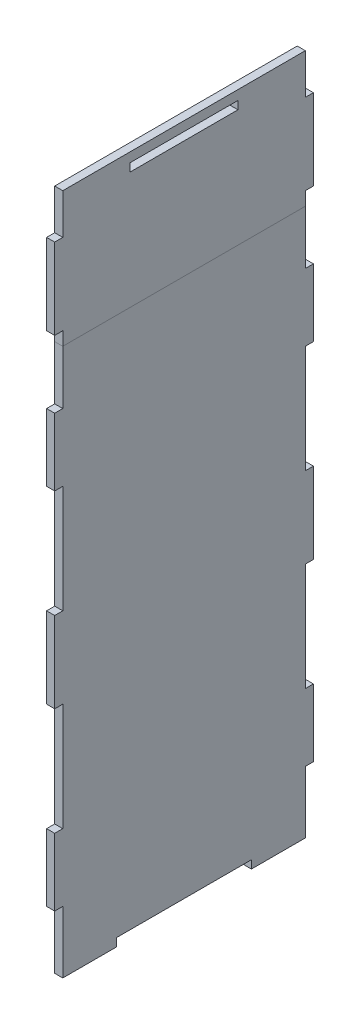
SolidWorks part; units mm, degrees
ref_plane "Front" through (0, 0, 0) normal (0, 0, 1) x (1, 0, 0)
ref_plane "Top" through (0, 0, 0) normal (0, 1, 0) x (1, 0, 0)
ref_plane "Right" through (0, 0, 0) normal (1, 0, 0) x (0, 0, -1)
sketch "Sketch1" plane through (0, 0, 0) normal (1, 0, 0) x (0, 0, -1)
  line L1 (0, 0) -> (90, 0)
  line L2 (0, 0) -> (0, 200)
  line L3 (0, 200) -> (90, 200)
  line L4 (90, 0) -> (90, 200)
  dimension "D1" = 200
  dimension "D2" = 90
extrude "Boss-Extrude1" add sketch "Sketch1" along normal blind 3
sketch "Sketch2" [suppressed] plane through (3, 0, 0) normal (1, 0, 0) x (0, 0, -1)
  line L0 (0, 0) -> (90, 0) construction
  line L1 (-3, 25) -> (0, 25)
  line L2 (-3, 25) -> (-3, 5)
  line L3 (-3, 5) -> (0, 5)
  line L4 (0, 25) -> (0, 5)
  line L5 (90, 25) -> (93, 25)
  line L6 (90, 25) -> (90, 5)
  line L7 (90, 5) -> (93, 5)
  line L8 (93, 25) -> (93, 5)
  line L9 (0, 200) -> (0, 0) construction
  line L10 (90, 0) -> (90, 200) construction
  line L12 (-3, 175) -> (0, 175)
  line L13 (-3, 175) -> (-3, 155)
  line L14 (-3, 155) -> (0, 155)
  line L15 (0, 175) -> (0, 155)
  line L16 (-3, 105) -> (0, 105)
  line L17 (-3, 105) -> (-3, 75)
  line L18 (-3, 75) -> (0, 75)
  line L19 (0, 105) -> (0, 75)
  line L20 (93, 175) -> (90, 175)
  line L21 (93, 175) -> (93, 155)
  line L22 (93, 155) -> (90, 155)
  line L23 (90, 175) -> (90, 155)
  line L24 (93, 105) -> (90, 105)
  line L25 (93, 105) -> (93, 75)
  line L26 (93, 75) -> (90, 75)
  line L27 (90, 105) -> (90, 75)
  dimension "D1" = 3
  dimension "D2" = 20
  dimension "D3" = 3
  dimension "D4" = 5
  dimension "D5" = 30
  dimension "D6" = 20
  dimension "D7" = 50
  dimension "D8" = 50
extrude "Boss-Extrude2" [suppressed] add sketch "Sketch2" against normal through all
sketch "Sketch3" [suppressed] plane through (3, 0, 0) normal (1, 0, 0) x (0, 0, -1)
  line L0 (10, 200) -> (15, 10)
  line L1 (15, 10) -> (75, 10)
  line L2 (75, 10) -> (80, 200)
  line L3 (80, 200) -> (10, 200)
  line L4 (90, 200) -> (0, 200) construction
  line L5 (0, 200) -> (0, 175) construction
  line L12 (0, 0) -> (90, 0) construction
  point P2 (45, 200)
  point P5 (45, 10)
  point P8 (45, 200)
  line M21 (90, 200) -> (0, 200)
  dimension "D1" = 10
  dimension "D2" = 15
  dimension "D3" = 10
extrude "Cut-Extrude1" [suppressed] cut sketch "Sketch3" against normal through all contours L1 L2 L0 M21
sketch "Sketch4" plane through (3, 0, 0) normal (1, 0, 0) x (0, 0, -1)
  line L0 (0, 200) -> (0, 0) construction
  line L1 (-3, 180) -> (0, 180)
  line L2 (-3, 180) -> (-3, 155)
  line L3 (-3, 155) -> (0, 155)
  line L4 (0, 180) -> (0, 155)
  line L5 (-3, 115) -> (0, 115)
  line L6 (-3, 115) -> (-3, 85)
  line L7 (-3, 85) -> (0, 85)
  line L8 (0, 115) -> (0, 85)
  line L9 (-3, 45) -> (0, 45)
  line L10 (-3, 45) -> (-3, 20)
  line L11 (-3, 20) -> (0, 20)
  line L12 (0, 45) -> (0, 20)
  line L13 (93, 20) -> (90, 20)
  line L14 (93, 20) -> (93, 45)
  line L15 (93, 45) -> (90, 45)
  line L16 (90, 20) -> (90, 45)
  line L17 (90, 85) -> (93, 85)
  line L18 (90, 85) -> (90, 115)
  line L19 (90, 115) -> (93, 115)
  line L20 (93, 85) -> (93, 115)
  line L21 (93, 155) -> (90, 155)
  line L22 (93, 155) -> (93, 180)
  line L23 (93, 180) -> (90, 180)
  line L24 (90, 155) -> (90, 180)
  line L25 (90, 0) -> (90, 200) construction
  line L26 (0, 0) -> (90, 0) construction
  line L27 (90, 200) -> (0, 200) construction
  point P28 (-3, 100)
  point P29 (0, 100)
  dimension "D1" = 3
  dimension "D5" = 30
  dimension "D6" = 20
  dimension "D2" = 3
  dimension "D3" = 25
  dimension "D4" = 25
  dimension "D7" = 20
extrude "Boss-Extrude3" add sketch "Sketch4" against normal through all
sketch "Sketch5" plane through (3, 0, 0) normal (1, 0, 0) x (0, 0, -1)
  line L0 (20, -1.5) -> (70, -1.5) construction
  line L1 (0, 0) -> (20, 0)
  line L2 (0, 0) -> (0, -3)
  line L3 (0, -3) -> (20, -3)
  line L4 (20, 0) -> (20, -3)
  line L5 (70, 0) -> (90, 0)
  line L6 (70, 0) -> (70, -3)
  line L7 (70, -3) -> (90, -3)
  line L8 (90, 0) -> (90, -3)
  line L9 (0, 0) -> (90, 0) construction
  point P13 (45, 0)
  point P14 (45, -1.5)
  dimension "D1" = 50
  dimension "D2" = 3
extrude "Boss-Extrude4" add sketch "Sketch5" against normal through all
sketch "Sketch6" plane through (3, 0, 0) normal (1, 0, 0) x (0, 0, -1)
  line L0 (90, 180) -> (90, 200) construction
  line L1 (0, 200) -> (90, 200)
  line L2 (0, 200) -> (0, 250)
  line L3 (0, 250) -> (90, 250)
  line L4 (90, 200) -> (90, 250)
  dimension "D1" = 50
extrude "Boss-Extrude5" add sketch "Sketch6" against normal blind 3 separate body
sketch "Sketch7" plane through (3, 0, 0) normal (1, 0, 0) x (0, 0, -1)
  line L0 (90, 250) -> (0, 250) construction
  line L1 (25, 243.5) -> (65, 243.5)
  line L2 (25, 243.5) -> (25, 246.5)
  line L3 (25, 246.5) -> (65, 246.5)
  line L4 (65, 243.5) -> (65, 246.5)
  point P4 (25, 245)
  point P5 (45, 246.5)
  point P8 (45, 250)
  dimension "D1" = 40
  dimension "D2" = 5
  dimension "D3" = 3
extrude "Cut-Extrude2" cut sketch "Sketch7" against normal blind 3
sketch "Sketch8" plane through (3, 0, 0) normal (1, 0, 0) x (0, 0, -1)
  line L0 (90, 200) -> (0, 200) construction
  line L1 (-3, 235) -> (0, 235)
  line L2 (-3, 235) -> (-3, 205)
  line L3 (-3, 205) -> (0, 205)
  line L4 (0, 235) -> (0, 205)
  line L5 (90, 235) -> (93, 235)
  line L6 (90, 235) -> (90, 205)
  line L7 (90, 205) -> (93, 205)
  line L8 (93, 235) -> (93, 205)
  line L9 (0, 250) -> (0, 200) construction
  line L10 (90, 200) -> (90, 250) construction
  dimension "D3" = 3
  dimension "D1" = 5
  dimension "D2" = 30
  dimension "D4" = 3
extrude "Boss-Extrude6" add sketch "Sketch8" against normal blind 3
equation "\"D3@Sketch2\"=\"D1@Sketch2\""
equation "\"D2@Sketch4\"=\"D1@Sketch4\""
equation "\"D4@Sketch4\"=\"D3@Sketch4\""
equation "\"D6@Sketch2\"=\"D2@Sketch2\""
equation "\"D4@Sketch8\"=\"D3@Sketch8\""
